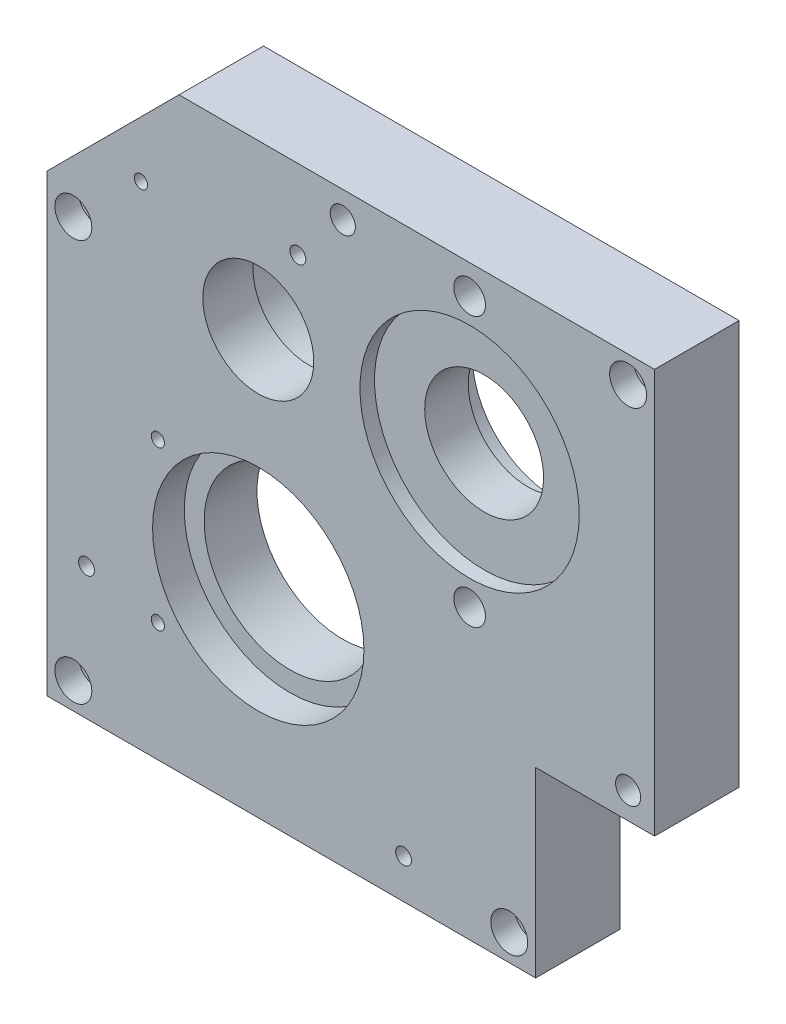
SolidWorks part; units mm, degrees
ref_plane "前视基准面" through (0, 0, 0) normal (0, 0, 1) x (1, 0, 0)
ref_plane "上视基准面" through (0, 0, 0) normal (0, 1, 0) x (1, 0, 0)
ref_plane "右视基准面" through (0, 0, 0) normal (1, 0, 0) x (0, 0, -1)
sketch "草图1" plane through (0, 0, 0) normal (0, 0, 1) x (1, 0, 0)
  line L18 (105, -80) -> (105, -6)
  line L19 (105, -6) -> (150, -6)
  line L20 (150, -6) -> (150, 147)
  line L21 (150, 147) -> (-30, 147)
  line L22 (-30, 147) -> (-80, 97)
  line L23 (-80, 97) -> (-80, -80)
  line L26 (-80, -80) -> (105, -80)
extrude "凸台-拉伸1" add sketch "草图1" along normal blind 32
sketch "草图3" plane through (0, 0, 32) normal (0, 0, 1) x (1, 0, 0)
  circle A0 centre (0, 0) radius 40
  dimension "D1" = 80
extrude "切除-拉伸1" cut sketch "草图3" against normal blind 12
sketch "草图4" plane through (0, 0, 20) normal (0, 0, 1) x (1, 0, 0)
  circle A0 centre (0, 0) radius 32.5
  dimension "D1" = 65
extrude "切除-拉伸2" cut sketch "草图4" against normal blind 113
sketch "草图5" plane through (0, 0, 0) normal (0, 0, -1) x (-1, 0, 0)
  circle A0 centre (0, 85) radius 23.5
  circle A1 centre (0, 0) radius 32.5 construction
  dimension "D1" = 85
  dimension "D2" = 47
extrude "切除-拉伸3" cut sketch "草图5" against normal blind 13
sketch "草图6" plane through (0, 0, 13) normal (0, 0, -1) x (-1, 0, 0)
  circle A0 centre (0, 85) radius 21
  dimension "D1" = 42
extrude "切除-拉伸4" cut sketch "草图6" against normal blind 113
sketch "草图7" plane through (0, 0, 0) normal (0, 0, -1) x (-1, 0, 0)
  circle A0 centre (-80, 85) radius 22.5
  circle A1 centre (0, 85) radius 21 construction
  dimension "D1" = 80
  dimension "D2" = 45
extrude "切除-拉伸5" cut sketch "草图7" against normal blind 40
sketch "草图8" plane through (0, 0, 32) normal (0, 0, 1) x (1, 0, 0)
  circle A0 centre (80, 85) radius 41.5
  dimension "D1" = 83
extrude "切除-拉伸6" cut sketch "草图8" against normal blind 5.5
sketch "草图9" plane through (0, 0, 0) normal (0, 0, -1) x (-1, 0, 0)
  circle A0 centre (-80, 85) radius 31
  dimension "D1" = 62
extrude "切除-拉伸7" cut sketch "草图9" against normal blind 10
sketch "草图10" plane through (0, 0, 0) normal (0, 0, -1) x (-1, 0, 0)
  circle A0 centre (-41, 85) radius 2.5
  circle A1 centre (-80, 85) radius 22.5 construction
  dimension "D1" = 5
  dimension "D2" = 39
extrude "切除-拉伸8" cut sketch "草图10" against normal blind 18
pattern_circular "阵列(圆周)1" count 4 over 360 about axis through (80, 85, 0) along (0, 0, 1) of "切除-拉伸8"
sketch "草图12" plane through (0, 0, 0) normal (0, 0, -1) x (-1, 0, 0)
  line L0 (80, 97) -> (80, -80) construction
  line L1 (-105, -80) -> (80, -80)
  line L2 (-105, -80) -> (-105, -75)
  line L3 (-105, -75) -> (80, -75)
  line L4 (80, -80) -> (80, -75)
  dimension "D1" = 5
extrude "切除-拉伸10" cut sketch "草图12" against normal blind 114
sketch "草图13" plane through (0, 0, 32) normal (0, 0, 1) x (1, 0, 0)
  line L0 (80, 85) -> (190.0192, 85) construction
  circle A0 centre (80, 34) radius 6
  circle A1 centre (80, 85) radius 22.5 construction
  circle A2 centre (80, 136) radius 6
  dimension "D1" = 12
  dimension "D2" = 51
extrude "切除-拉伸11" cut sketch "草图13" against normal blind 14
sketch "草图14" plane through (0, 0, 32) normal (0, 0, 1) x (1, 0, 0)
  line L0 (150, -6) -> (150, 147) construction
  line L1 (150, 147) -> (-30, 147) construction
  line L2 (105, -75) -> (105, -6) construction
  line L3 (105, -75) -> (-80, -75) construction
  line L4 (-80, 97) -> (-80, -75) construction
  line L5 (105, -6) -> (150, -6) construction
  circle A0 centre (140, 137) radius 4
  circle A1 centre (140, 4) radius 4.76
  circle A2 centre (32, 137) radius 4.76
  circle A3 centre (-70, -65) radius 4
  circle A4 centre (95, -65) radius 4
  circle A5 centre (-70, 87) radius 4
  dimension "D1" = 8
  dimension "D2" = 8
  dimension "D3" = 8
  dimension "D4" = 8
  dimension "D5" = 10
  dimension "D6" = 10
  dimension "D8" = 10
  dimension "D9" = 10
  dimension "D10" = 10
  dimension "D11" = 10
  dimension "D12" = 10
  dimension "D13" = 9.52
  dimension "D14" = 9.52
  dimension "D15" = 10
  dimension "D16" = 10
  dimension "D17" = 10
  dimension "D18" = 62
  dimension "D7" = 10
extrude "切除-拉伸12" cut sketch "草图14" against normal blind 96
sketch "草图15" plane through (0, 0, 32) normal (0, 0, 1) x (1, 0, 0)
  circle A0 centre (140, 137) radius 7
  circle A1 centre (95, -65) radius 7
  circle A2 centre (-70, -65) radius 7
  circle A3 centre (-70, 87) radius 7
  dimension "D1" = 14
  dimension "D2" = 14
  dimension "D3" = 14
  dimension "D4" = 14
extrude "切除-拉伸13" cut sketch "草图15" against normal blind 9
sketch "草图16" plane through (0, 0, 32) normal (0, 0, 1) x (1, 0, 0)
  circle A0 centre (-44.3934, 111.3934) radius 2.531
  circle A1 centre (55, -60) radius 3
  circle A2 centre (-65, -25) radius 3
  circle A3 centre (15, 117) radius 3
  circle A4 centre (15, 117) radius 3 construction
  circle A5 centre (-44.3934, 111.3934) radius 2.531 construction
  circle A6 centre (55, -60) radius 3 construction
  circle A7 centre (-65, -25) radius 3 construction
extrude "切除-拉伸14" cut sketch "草图16" against normal blind 10
sketch "草图17" plane through (0, 0, 32) normal (0, 0, 1) x (1, 0, 0)
  line L0 (0, 0) -> (-103.3041, 0) construction
  circle A0 centre (-38, 30) radius 2.5
  circle A1 centre (-38, -30) radius 2.5
  dimension "D2" = 30
  dimension "D3" = 5
  dimension "D1" = 38
extrude "切除-拉伸15" cut sketch "草图17" against normal blind 8
